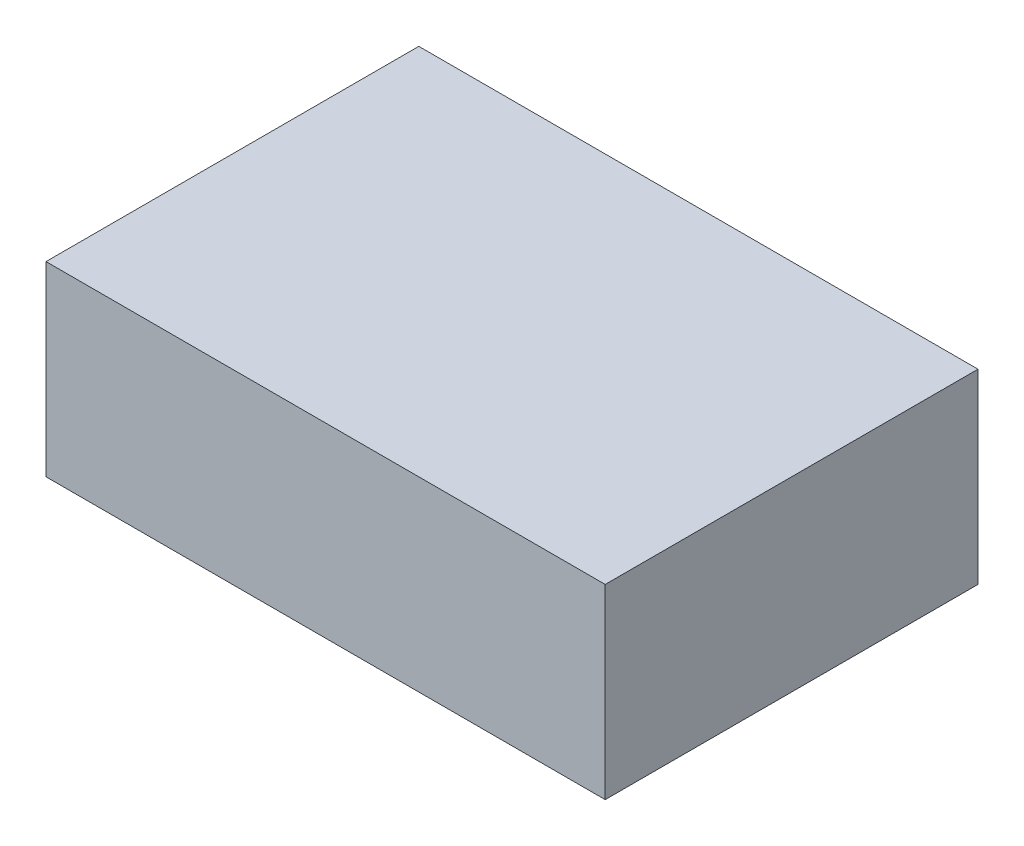
SolidWorks part; units mm, degrees
ref_plane "Front Plane" through (0, 0, 0) normal (0, 0, 1) x (1, 0, 0)
ref_plane "Top Plane" through (0, 0, 0) normal (0, 1, 0) x (1, 0, 0)
ref_plane "Right Plane" through (0, 0, 0) normal (1, 0, 0) x (0, 0, -1)
sketch "Sketch1" plane through (0, 0, 0) normal (0, 1, 0) x (1, 0, 0)
  line L1 (0, 0.5) -> (0.75, 0.5)
  line L2 (0, 0.5) -> (0, 0)
  line L3 (0, 0) -> (0.75, 0)
  line L4 (0.75, 0.5) -> (0.75, 0)
  point P4 (0, 0)
  dimension "D1" = 0.75
  dimension "D2" = 0.5
extrude "Boss-Extrude1" add sketch "Sketch1" along normal blind 0.25
